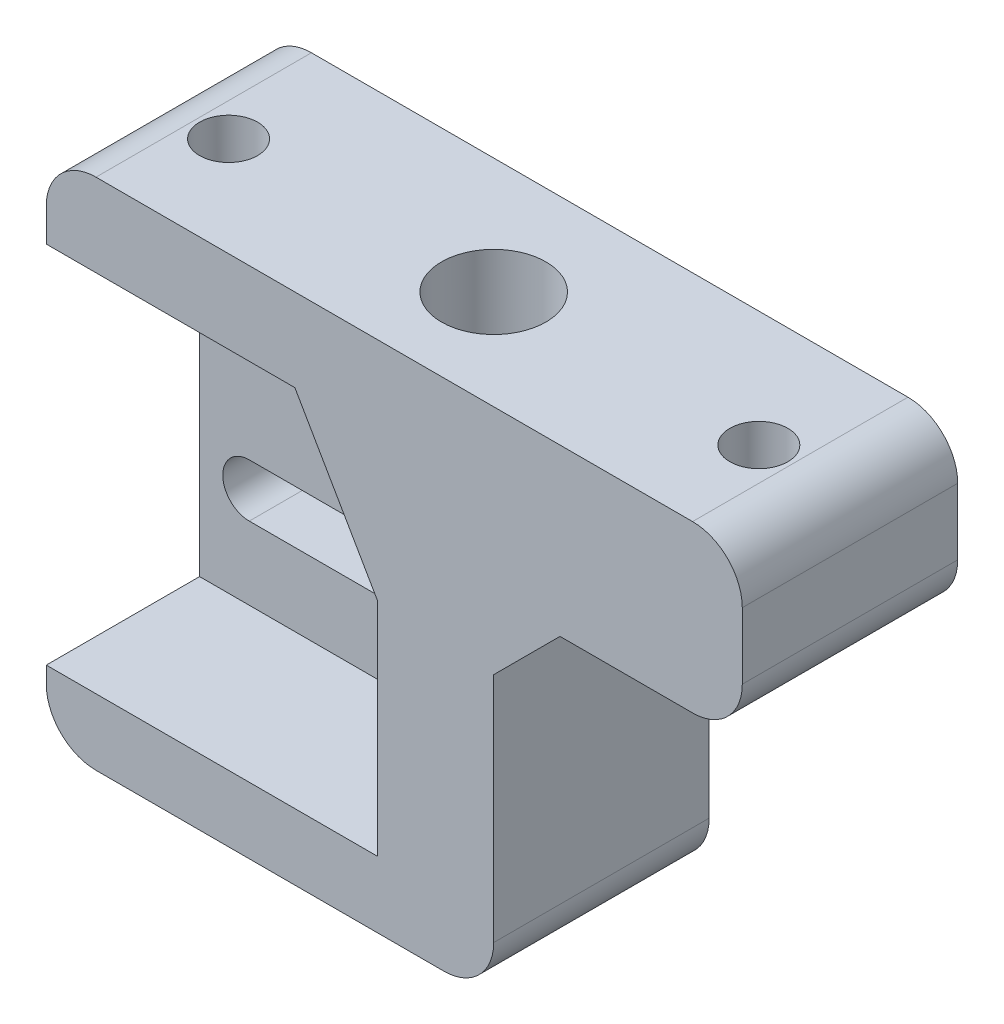
SolidWorks part; units mm, degrees
ref_plane "Plan de face" through (0, 0, 0) normal (0, 0, 1) x (1, 0, 0)
ref_plane "Plan de dessus" through (0, 0, 0) normal (0, 1, 0) x (1, 0, 0)
ref_plane "Plan de droite" through (0, 0, 0) normal (1, 0, 0) x (0, 0, -1)
sketch "Esquisse1" plane through (0, 0, 0) normal (0, 0, 1) x (1, 0, 0)
  line L1 (0, 0) -> (30, 0)
  line L2 (0, 0) -> (0, 40)
  line L3 (0, 40) -> (30, 40)
  line L4 (30, 0) -> (30, 40)
  dimension "D1" = 30
  dimension "D2" = 40
extrude "Boss.-Extru.1" add sketch "Esquisse1" along normal blind 14
sketch "Esquisse3" plane through (0, 40, 0) normal (0, 1, 0) x (1, 0, 0)
  line L0 (24, 0) -> (24, -14) construction
  line L3 (30, -14) -> (30, 0) construction
  line L4 (30, -14) -> (0, -14) construction
  line L5 (30, 0) -> (0, 0) construction
  circle A0 centre (24, -7) radius 3.15
  dimension "D1" = 6.3
  dimension "D2" = 6
extrude "Enlèv. mat.-Extru.1" cut sketch "Esquisse3" against normal blind 30
sketch "Esquisse4" plane through (0, 0, 14) normal (0, 0, 1) x (1, 0, 0)
  line L0 (0, 40) -> (0, 0) construction
  line L1 (0, 13) -> (15, 13)
  line L2 (0, 13) -> (0, 35)
  line L3 (0, 35) -> (15, 35)
  line L4 (15, 13) -> (15, 35)
  line L5 (30, 40) -> (0, 40) construction
  dimension "D1" = 15
  dimension "D2" = 22
  dimension "D3" = 5
extrude "Enlèv. mat.-Extru.2" cut sketch "Esquisse4" against normal blind 10.25
sketch "Esquisse5" plane through (0, 0, 3.75) normal (0, 0, 1) x (1, 0, 0)
  line L0 (15, 24) -> (0, 24) construction
  line L1 (15, 13) -> (15, 35) construction
  line L2 (0, 35) -> (0, 13) construction
  line L3 (10, 24) -> (10, 35) construction
  line L4 (15, 35) -> (0, 35) construction
  line L5 (6, 29) -> (14, 29) construction
  line L6 (6, 30.6) -> (14, 30.6)
  line L7 (6, 27.4) -> (14, 27.4)
  line L8 (6, 19) -> (14, 19) construction
  line L9 (6, 17.4) -> (14, 17.4)
  line L10 (6, 20.6) -> (14, 20.6)
  arc A0 (6, 30.6) -> (6, 27.4) centre (6, 29) ccw
  arc A1 (6, 17.4) -> (6, 20.6) centre (6, 19) cw
  arc A2 (14, 27.4) -> (14, 30.6) centre (14, 29) ccw
  arc A3 (14, 20.6) -> (14, 17.4) centre (14, 19) cw
  point P14 (10, 29)
  point P19 (10, 19)
  dimension "D2" = 5
  dimension "D3" = 10
  dimension "D1" = 1.6
  dimension "D4" = 8
extrude "Enlèv. mat.-Extru.3" cut sketch "Esquisse5" against normal through all
sketch "Esquisse6" plane through (0, 0, 14) normal (0, 0, 1) x (1, 0, 0)
  line L0 (15, 35) -> (18, 35)
  line L1 (15, 13) -> (15, 17.751) construction
  line L2 (23, 26.3397) -> (23, 13)
  line L3 (23, 13) -> (15, 13)
  line L4 (15, 13) -> (15, 35)
  line L5 (15, 13) -> (15, 35) construction
  line L6 (15, 35) -> (0, 35) construction
  line L7 (18, 35) -> (23, 26.3397)
  dimension "D1" = 30
  dimension "D2" = 3
  dimension "D3" = 8
extrude "Enlèv. mat.-Extru.4" cut sketch "Esquisse6" against normal up to surface (10.25 mm away) up to face at (10.4325, 24, 3.75)
sketch "Esquisse7" plane through (0, 0, 14) normal (0, 0, 1) x (1, 0, 0)
  line L0 (0, 6.5) -> (30, 6.5) construction
  line L1 (0, 13) -> (0, 0) construction
  line L2 (30, 0) -> (30, 40) construction
  line L3 (15, 6.5) -> (15, 0) construction
  line L4 (0, 0) -> (30, 0) construction
  circle A0 centre (5, 6.5) radius 1.75
  circle A1 centre (25, 6.5) radius 1.75
  dimension "D1" = 3.5
  dimension "D2" = 10
extrude "Enlèv. mat.-Extru.5" cut sketch "Esquisse7" against normal through all
sketch "Esquisse9" plane through (0, 40, 0) normal (0, 1, 0) x (1, 0, 0)
  line L0 (0, -14) -> (0, 0) construction
  line L1 (30, -14) -> (0, -14)
  line L2 (30, -14) -> (30, -13)
  line L3 (30, -13) -> (0, -13)
  line L4 (0, -14) -> (0, -13)
  dimension "D1" = 1
extrude "Enlèv. mat.-Extru.9" cut sketch "Esquisse9" against normal up to vertex
sketch "Esquisse11" plane through (0, 0, 13) normal (0, 0, 1) x (1, 0, 0)
  line L0 (30, 0) -> (30, 40) construction
  line L1 (0, 0) -> (30, 0)
  line L2 (0, 0) -> (0, 9)
  line L3 (0, 9) -> (30, 9)
  line L4 (30, 0) -> (30, 9)
  dimension "D1" = 9
extrude "Enlèv. mat.-Extru.10" cut sketch "Esquisse11" against normal up to vertex
sketch "Esquisse12" plane through (0, 40, 0) normal (0, 1, 0) x (1, 0, 0)
  line L0 (30, 0) -> (0, 0) construction
  line L1 (30, -13) -> (45, -13)
  line L2 (30, -13) -> (30, 0)
  line L3 (30, 0) -> (45, 0)
  line L4 (45, -13) -> (45, 0)
  dimension "D1" = 15
extrude "Boss.-Extru.2" add sketch "Esquisse12" against normal blind 10
sketch "Esquisse13" plane through (0, 40, 0) normal (0, 1, 0) x (1, 0, 0)
  line L0 (24, -7) -> (40, -7) construction
  line L1 (24, -7) -> (24, -1.0006) construction
  circle A0 centre (40, -7) radius 1.75
  circle A1 centre (8, -7) radius 1.75
  dimension "D1" = 3.5
  dimension "D2" = 16
extrude "Enlèv. mat.-Extru.11" cut sketch "Esquisse13" against normal blind 12
chamfer "Chanfrein1" distance 4 angle 45 1 edges at (30, 30, 6.5)
sketch "Esquisse14" plane through (0, 0, 13) normal (0, 0, 1) x (1, 0, 0)
  line L0 (45, 40) -> (0, 40) construction
  line L1 (0, 9) -> (3, 9)
  line L2 (0, 9) -> (0, 40)
  line L3 (0, 40) -> (3, 40)
  line L4 (3, 9) -> (3, 40)
  dimension "D1" = 3
extrude "Enlèv. mat.-Extru.12" cut sketch "Esquisse14" against normal through all both and the other way through all
fillet "Congé1" radius 3 5 edges at (45, 40, 6.5) (45, 30, 6.5) (30, 9, 6.5) (3, 9, 6.5) (3, 40, 6.5)
